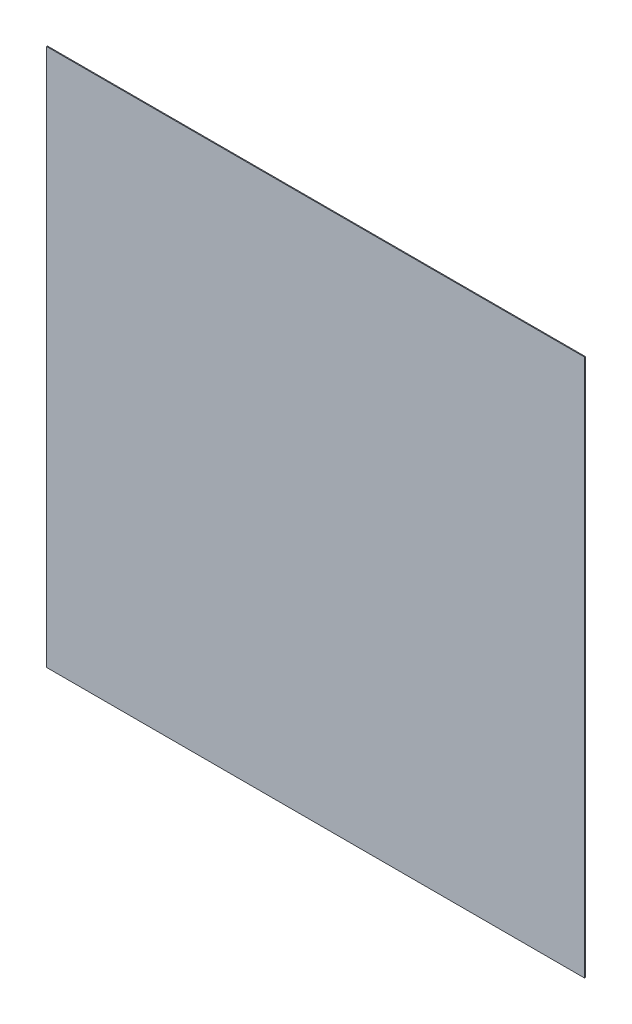
SolidWorks part; units mm, degrees
ref_plane "Front Plane" through (0, 0, 0) normal (0, 0, 1) x (1, 0, 0)
ref_plane "Top Plane" through (0, 0, 0) normal (0, 1, 0) x (1, 0, 0)
ref_plane "Right Plane" through (0, 0, 0) normal (1, 0, 0) x (0, 0, -1)
sketch "Sketch1" plane through (0, 0, 0) normal (0, 0, 1) x (1, 0, 0)
  line L0 (-1.8669, 0) -> (1.8669, 0) construction
  line L1 (152.4, -152.4) -> (-152.4, -152.4) construction
  line L2 (152.4, -152.4) -> (152.4, 152.4) construction
  line L3 (152.4, 152.4) -> (-152.4, 152.4) construction
  line L4 (-152.4, -152.4) -> (-152.4, 152.4) construction
  line L5 (152.4, -152.4) -> (-152.4, 152.4) construction
  line L6 (152.4, 152.4) -> (-152.4, -152.4) construction
  point P0 (0, 0)
  dimension "Sheet Length" = 304.8
  dimension "Sheet Width" = 304.8
  dimension "Opening Size" = 3.7338
sketch "Sketch2" plane through (0, 0, 0) normal (1, 0, 0) x (0, 0, -1)
  line L0 (-0.254, 0) -> (0.254, 0) construction
  dimension "Wire Diameter" = 0.508
sketch "Sketch3" plane through (0, 0, 0) normal (0, 0, 1) x (1, 0, 0)
  line L1 (-152.4, 152.4) -> (152.4, 152.4)
  line L2 (-152.4, 152.4) -> (-152.4, -152.4)
  line L3 (-152.4, -152.4) -> (152.4, -152.4)
  line L4 (152.4, 152.4) -> (152.4, -152.4)
extrude "Boss-Extrude1" add sketch "Sketch3" against normal up to vertex (0.254 mm away) and the other way up to vertex (0.254 mm away) up to point (0, 0, -0.254) other way up to point (0, 0, 0.254)
sketch "Reference Sketch1" plane through (0, 0, 0) normal (0, 0, 1) x (1, 0, 0)
  line L0 (-152.4, 0) -> (152.4, 0) construction
  line L1 (-152.4, -152.4) -> (-152.4, 152.4) construction
  line L2 (152.4, -152.4) -> (152.4, 152.4) construction
  line L3 (0, 152.4) -> (0, -152.4) construction
  line L4 (152.4, 152.4) -> (-152.4, 152.4) construction
  line L5 (152.4, -152.4) -> (-152.4, -152.4) construction
  point P12 (-108.8571, 0)
  point P13 (-65.3143, 0)
  point P14 (-21.7714, 0)
  point P15 (21.7714, 0)
  point P16 (65.3143, 0)
  point P17 (108.8571, 0)
  point P18 (0, 118.5333)
  point P24 (65.3143, -118.5333)
  point P27 (0, 84.6667)
  point P28 (0, 50.8)
  point P29 (0, 16.9333)
  point P30 (0, -16.9333)
  point P31 (0, -50.8)
  point P32 (0, -84.6667)
  point P33 (0, -118.5333)
